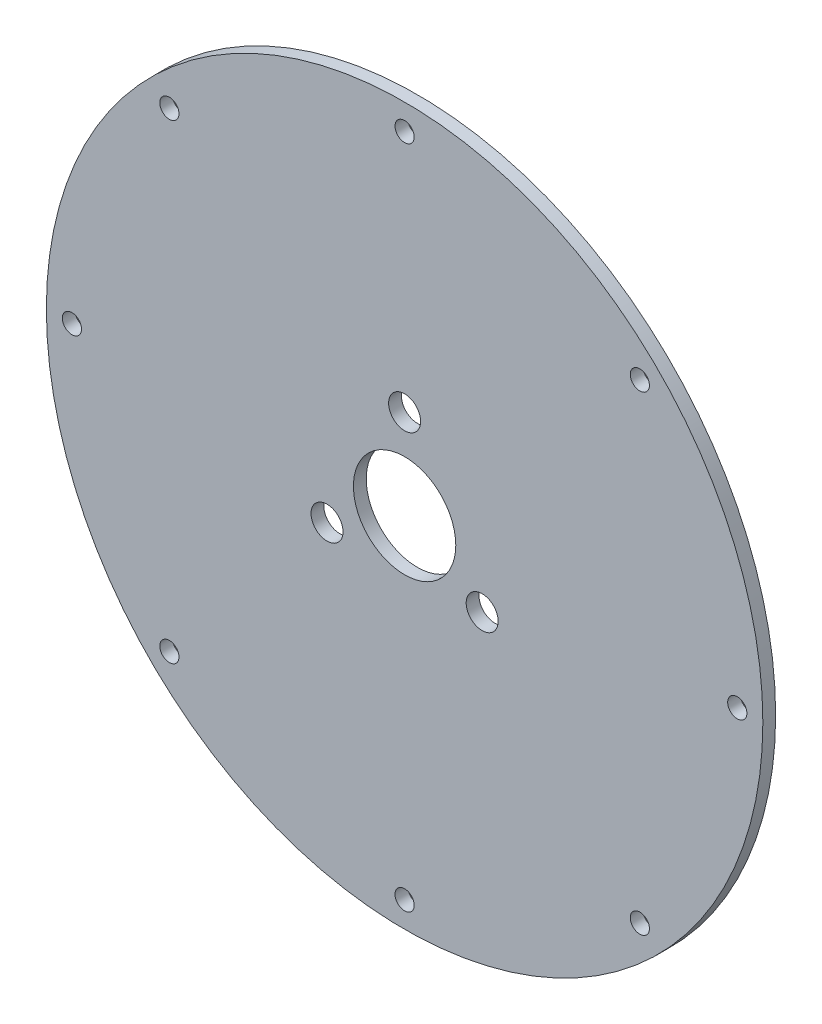
SolidWorks part; units mm, degrees
material "6061 Alloy"
ref_plane "Front Plane" through (0, 0, 0) normal (0, 0, 1) x (1, 0, 0)
ref_plane "Top Plane" through (0, 0, 0) normal (0, 1, 0) x (1, 0, 0)
ref_plane "Right Plane" through (0, 0, 0) normal (1, 0, 0) x (0, 0, -1)
sketch "Sketch1" plane through (0, 0, 0) normal (0, 0, 1) x (1, 0, 0)
  circle A0 centre (0, 0) radius 88.9
  circle A1 centre (0, 0) radius 22.225 construction
  circle A2 centre (0, 22.225) radius 3.9688
  circle A3 centre (19.2474, -11.1125) radius 3.9687
  circle A4 centre (-19.2474, -11.1125) radius 3.9688
  circle A5 centre (0, 0) radius 82.55 construction
  circle A6 centre (0, 82.55) radius 2.3812
  circle A7 centre (58.3717, 58.3717) radius 2.3812
  circle A8 centre (82.55, 0) radius 2.3813
  circle A9 centre (58.3717, -58.3717) radius 2.3812
  circle A10 centre (0, -82.55) radius 2.3812
  circle A11 centre (-58.3717, -58.3717) radius 2.3812
  circle A12 centre (-82.55, 0) radius 2.3813
  circle A13 centre (-58.3717, 58.3717) radius 2.3812
  circle A14 centre (0, 0) radius 12.7
  point P12 (0, 0)
  point P38 (0, 0)
  dimension "D1" = 177.8
  dimension "D2" = 44.45
  dimension "D3" = 7.9375
  dimension "D5" = 165.1
  dimension "D6" = 4.7625
  dimension "D4" = 3
  dimension "D7" = 8
extrude "Boss-Extrude1" add sketch "Sketch1" along normal blind 3.175
sketch "Sketch2" plane through (0, 0, 0) normal (0, 1, 0) x (1, 0, 0)
  line L0 (0, 0) -> (0, -62.4062)
